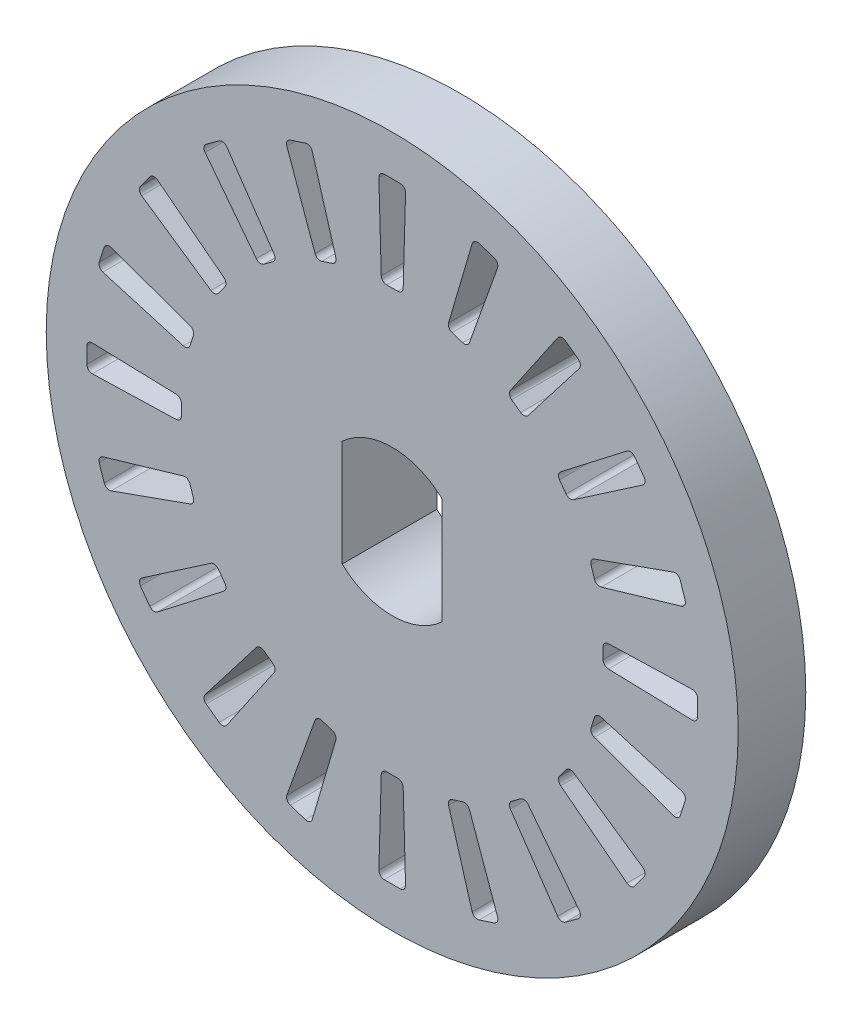
SolidWorks part; units mm, degrees
ref_plane "Alzado" through (0, 0, 0) normal (0, 0, 1) x (1, 0, 0)
ref_plane "Planta" through (0, 0, 0) normal (0, 1, 0) x (1, 0, 0)
ref_plane "Vista lateral" through (0, 0, 0) normal (1, 0, 0) x (0, 0, -1)
sketch "Croquis1" plane through (0, 0, 0) normal (0, 0, 1) x (1, 0, 0)
  line L0 (0, -5.4392) -> (0, 5.4392) construction
  line L1 (1.85, -1.9666) -> (1.85, 1.9666)
  line L2 (-1.85, -1.9666) -> (-1.85, 1.9666)
  line L3 (-1.85, -5.4392) -> (-1.85, 5.4392) construction
  line L4 (1.85, -5.4392) -> (1.85, 5.4392) construction
  circle A0 centre (0, 0) radius 12.8
  arc A1 (-1.85, -1.9666) -> (1.85, -1.9666) centre (0, 0) ccw
  arc A2 (1.85, 1.9666) -> (-1.85, 1.9666) centre (0, 0) ccw
  point P7 (0, 0)
  dimension "D1" = 25.6
  dimension "D2" = 5.4
  dimension "D3" = 1.85
  dimension "D4" = 1.85
extrude "Saliente-Extruir1" add sketch "Croquis1" along normal blind 2.5
sketch "Croquis2" plane through (0, 0, 0) normal (0, 0, 1) x (1, 0, 0)
  line L0 (-16.679, 12.8) -> (19.2749, 12.8) construction
  line L1 (0.2056, 7.8) -> (-0.2056, 7.8)
  line L2 (2.6059, 7.3547) -> (2.2148, 7.4818)
  line L3 (0.2942, 11.3) -> (-0.2942, 11.3)
  line L4 (3.7717, 10.656) -> (3.2121, 10.8379)
  line L5 (0.5, 7.8) -> (-0.5, 11.3) construction
  line L6 (0.5, 11.3) -> (-0.5, 7.8) construction
  line L7 (2.9584, 10.704) -> (2.0847, 7.7283)
  line L8 (3.8983, 10.3986) -> (2.8561, 7.4777)
  line L9 (-0.4941, 11.0943) -> (-0.4056, 7.9943)
  line L10 (0.4941, 11.0943) -> (0.4056, 7.9943)
  line L11 (2.8859, 7.2637) -> (3.0164, 10.9014) construction
  line L12 (3.9674, 10.5924) -> (1.9348, 7.5727) construction
  line L13 (4.7511, 6.1895) -> (4.4184, 6.4312)
  line L14 (6.88, 8.969) -> (6.404, 9.3148)
  line L15 (6.1213, 9.2659) -> (4.3708, 6.7059)
  line L16 (6.9208, 8.685) -> (5.027, 6.2291)
  line L17 (4.9892, 6.0164) -> (6.2375, 9.4358) construction
  line L18 (7.0465, 8.848) -> (4.1802, 6.6042) construction
  line L19 (6.4312, 4.4184) -> (6.1895, 4.7511)
  line L20 (9.3148, 6.404) -> (8.969, 6.88)
  line L21 (8.685, 6.9208) -> (6.2291, 5.027)
  line L22 (9.2659, 6.1213) -> (6.7059, 4.3708)
  line L23 (6.6042, 4.1802) -> (8.848, 7.0465) construction
  line L24 (9.4358, 6.2375) -> (6.0164, 4.9892) construction
  line L25 (7.4818, 2.2148) -> (7.3547, 2.6059)
  line L26 (10.8379, 3.2121) -> (10.656, 3.7717)
  line L27 (10.3986, 3.8983) -> (7.4777, 2.8561)
  line L28 (10.704, 2.9584) -> (7.7283, 2.0847)
  line L29 (7.5727, 1.9348) -> (10.5924, 3.9674) construction
  line L30 (10.9014, 3.0164) -> (7.2637, 2.8859) construction
  line L31 (7.8, -0.2056) -> (7.8, 0.2056)
  line L32 (11.3, -0.2942) -> (11.3, 0.2942)
  line L33 (11.0943, 0.4941) -> (7.9943, 0.4056)
  line L34 (11.0943, -0.4941) -> (7.9943, -0.4056)
  line L35 (7.8, -0.5) -> (11.3, 0.5) construction
  line L36 (11.3, -0.5) -> (7.8, 0.5) construction
  line L37 (7.3547, -2.6059) -> (7.4818, -2.2148)
  line L38 (10.656, -3.7717) -> (10.8379, -3.2121)
  line L39 (10.704, -2.9584) -> (7.7283, -2.0847)
  line L40 (10.3986, -3.8983) -> (7.4777, -2.8561)
  line L41 (7.2637, -2.8859) -> (10.9014, -3.0164) construction
  line L42 (10.5924, -3.9674) -> (7.5727, -1.9348) construction
  line L43 (6.1895, -4.7511) -> (6.4312, -4.4184)
  line L44 (8.969, -6.88) -> (9.3148, -6.404)
  line L45 (9.2659, -6.1213) -> (6.7059, -4.3708)
  line L46 (8.685, -6.9208) -> (6.2291, -5.027)
  line L47 (6.0164, -4.9892) -> (9.4358, -6.2375) construction
  line L48 (8.848, -7.0465) -> (6.6042, -4.1802) construction
  line L49 (4.4184, -6.4312) -> (4.7511, -6.1895)
  line L50 (6.404, -9.3148) -> (6.88, -8.969)
  line L51 (6.9208, -8.685) -> (5.027, -6.2291)
  line L52 (6.1213, -9.2659) -> (4.3708, -6.7059)
  line L53 (4.1802, -6.6042) -> (7.0465, -8.848) construction
  line L54 (6.2375, -9.4358) -> (4.9892, -6.0164) construction
  line L55 (2.2148, -7.4818) -> (2.6059, -7.3547)
  line L56 (3.2121, -10.8379) -> (3.7717, -10.656)
  line L57 (3.8983, -10.3986) -> (2.8561, -7.4777)
  line L58 (2.9584, -10.704) -> (2.0847, -7.7283)
  line L59 (1.9348, -7.5727) -> (3.9674, -10.5924) construction
  line L60 (3.0164, -10.9014) -> (2.8859, -7.2637) construction
  line L61 (-0.2056, -7.8) -> (0.2056, -7.8)
  line L62 (-0.2942, -11.3) -> (0.2942, -11.3)
  line L63 (0.4941, -11.0943) -> (0.4056, -7.9943)
  line L64 (-0.4941, -11.0943) -> (-0.4056, -7.9943)
  line L65 (-0.5, -7.8) -> (0.5, -11.3) construction
  line L66 (-0.5, -11.3) -> (0.5, -7.8) construction
  line L67 (-2.6059, -7.3547) -> (-2.2148, -7.4818)
  line L68 (-3.7717, -10.656) -> (-3.2121, -10.8379)
  line L69 (-2.9584, -10.704) -> (-2.0847, -7.7283)
  line L70 (-3.8983, -10.3986) -> (-2.8561, -7.4777)
  line L71 (-2.8859, -7.2637) -> (-3.0164, -10.9014) construction
  line L72 (-3.9674, -10.5924) -> (-1.9348, -7.5727) construction
  line L73 (-4.7511, -6.1895) -> (-4.4184, -6.4312)
  line L74 (-6.88, -8.969) -> (-6.404, -9.3148)
  line L75 (-6.1213, -9.2659) -> (-4.3708, -6.7059)
  line L76 (-6.9208, -8.685) -> (-5.027, -6.2291)
  line L77 (-4.9892, -6.0164) -> (-6.2375, -9.4358) construction
  line L78 (-7.0465, -8.848) -> (-4.1802, -6.6042) construction
  line L79 (-6.4312, -4.4184) -> (-6.1895, -4.7511)
  line L80 (-9.3148, -6.404) -> (-8.969, -6.88)
  line L81 (-8.685, -6.9208) -> (-6.2291, -5.027)
  line L82 (-9.2659, -6.1213) -> (-6.7059, -4.3708)
  line L83 (-6.6042, -4.1802) -> (-8.848, -7.0465) construction
  line L84 (-9.4358, -6.2375) -> (-6.0164, -4.9892) construction
  line L85 (-7.4818, -2.2148) -> (-7.3547, -2.6059)
  line L86 (-10.8379, -3.2121) -> (-10.656, -3.7717)
  line L87 (-10.3986, -3.8983) -> (-7.4777, -2.8561)
  line L88 (-10.704, -2.9584) -> (-7.7283, -2.0847)
  line L89 (-7.5727, -1.9348) -> (-10.5924, -3.9674) construction
  line L90 (-10.9014, -3.0164) -> (-7.2637, -2.8859) construction
  line L91 (-7.8, 0.2056) -> (-7.8, -0.2056)
  line L92 (-11.3, 0.2942) -> (-11.3, -0.2942)
  line L93 (-11.0943, -0.4941) -> (-7.9943, -0.4056)
  line L94 (-11.0943, 0.4941) -> (-7.9943, 0.4056)
  line L95 (-7.8, 0.5) -> (-11.3, -0.5) construction
  line L96 (-11.3, 0.5) -> (-7.8, -0.5) construction
  line L97 (-7.3547, 2.6059) -> (-7.4818, 2.2148)
  line L98 (-10.656, 3.7717) -> (-10.8379, 3.2121)
  line L99 (-10.704, 2.9584) -> (-7.7283, 2.0847)
  line L100 (-10.3986, 3.8983) -> (-7.4777, 2.8561)
  line L101 (-7.2637, 2.8859) -> (-10.9014, 3.0164) construction
  line L102 (-10.5924, 3.9674) -> (-7.5727, 1.9348) construction
  line L103 (-6.1895, 4.7511) -> (-6.4312, 4.4184)
  line L104 (-8.969, 6.88) -> (-9.3148, 6.404)
  line L105 (-9.2659, 6.1213) -> (-6.7059, 4.3708)
  line L106 (-8.685, 6.9208) -> (-6.2291, 5.027)
  line L107 (-6.0164, 4.9892) -> (-9.4358, 6.2375) construction
  line L108 (-8.848, 7.0465) -> (-6.6042, 4.1802) construction
  line L109 (-4.4184, 6.4312) -> (-4.7511, 6.1895)
  line L110 (-6.404, 9.3148) -> (-6.88, 8.969)
  line L111 (-6.9208, 8.685) -> (-5.027, 6.2291)
  line L112 (-6.1213, 9.2659) -> (-4.3708, 6.7059)
  line L113 (-4.1802, 6.6042) -> (-7.0465, 8.848) construction
  line L114 (-6.2375, 9.4358) -> (-4.9892, 6.0164) construction
  line L115 (-2.2148, 7.4818) -> (-2.6059, 7.3547)
  line L116 (-3.2121, 10.8379) -> (-3.7717, 10.656)
  line L117 (-3.8983, 10.3986) -> (-2.8561, 7.4777)
  line L118 (-2.9584, 10.704) -> (-2.0847, 7.7283)
  line L119 (-1.9348, 7.5727) -> (-3.9674, 10.5924) construction
  line L120 (-3.0164, 10.9014) -> (-2.8859, 7.2637) construction
  arc A0 (0.2056, 7.8) -> (0.4056, 7.9943) centre (0.2056, 8) ccw
  circle A1 centre (0, 0) radius 12.8 construction
  arc A2 (-0.2056, 7.8) -> (-0.4056, 7.9943) centre (-0.2056, 8) cw
  arc A3 (0.4941, 11.0943) -> (0.2942, 11.3) centre (0.2942, 11.1) ccw
  arc A4 (-0.2942, 11.3) -> (-0.4941, 11.0943) centre (-0.2942, 11.1) ccw
  arc A5 (2.6059, 7.3547) -> (2.8561, 7.4777) centre (2.6677, 7.5449) ccw
  arc A6 (2.2148, 7.4818) -> (2.0847, 7.7283) centre (2.2766, 7.672) cw
  arc A7 (3.8983, 10.3986) -> (3.7717, 10.656) centre (3.7099, 10.4658) ccw
  arc A8 (3.2121, 10.8379) -> (2.9584, 10.704) centre (3.1503, 10.6476) ccw
  arc A9 (4.7511, 6.1895) -> (5.027, 6.2291) centre (4.8686, 6.3513) ccw
  arc A10 (4.4184, 6.4312) -> (4.3708, 6.7059) centre (4.5359, 6.593) cw
  arc A11 (6.9208, 8.685) -> (6.88, 8.969) centre (6.7624, 8.8072) ccw
  arc A12 (6.404, 9.3148) -> (6.1213, 9.2659) centre (6.2864, 9.153) ccw
  arc A13 (6.4312, 4.4184) -> (6.7059, 4.3708) centre (6.593, 4.5359) ccw
  arc A14 (6.1895, 4.7511) -> (6.2291, 5.027) centre (6.3513, 4.8686) cw
  arc A15 (9.2659, 6.1213) -> (9.3148, 6.404) centre (9.153, 6.2864) ccw
  arc A16 (8.969, 6.88) -> (8.685, 6.9208) centre (8.8072, 6.7624) ccw
  arc A17 (7.4818, 2.2148) -> (7.7283, 2.0847) centre (7.672, 2.2766) ccw
  arc A18 (7.3547, 2.6059) -> (7.4777, 2.8561) centre (7.5449, 2.6677) cw
  arc A19 (10.704, 2.9584) -> (10.8379, 3.2121) centre (10.6476, 3.1503) ccw
  arc A20 (10.656, 3.7717) -> (10.3986, 3.8983) centre (10.4658, 3.7099) ccw
  arc A21 (7.8, -0.2056) -> (7.9943, -0.4056) centre (8, -0.2056) ccw
  arc A22 (7.8, 0.2056) -> (7.9943, 0.4056) centre (8, 0.2056) cw
  arc A23 (11.0943, -0.4941) -> (11.3, -0.2942) centre (11.1, -0.2942) ccw
  arc A24 (11.3, 0.2942) -> (11.0943, 0.4941) centre (11.1, 0.2942) ccw
  arc A25 (7.3547, -2.6059) -> (7.4777, -2.8561) centre (7.5449, -2.6677) ccw
  arc A26 (7.4818, -2.2148) -> (7.7283, -2.0847) centre (7.672, -2.2766) cw
  arc A27 (10.3986, -3.8983) -> (10.656, -3.7717) centre (10.4658, -3.7099) ccw
  arc A28 (10.8379, -3.2121) -> (10.704, -2.9584) centre (10.6476, -3.1503) ccw
  arc A29 (6.1895, -4.7511) -> (6.2291, -5.027) centre (6.3513, -4.8686) ccw
  arc A30 (6.4312, -4.4184) -> (6.7059, -4.3708) centre (6.593, -4.5359) cw
  arc A31 (8.685, -6.9208) -> (8.969, -6.88) centre (8.8072, -6.7624) ccw
  arc A32 (9.3148, -6.404) -> (9.2659, -6.1213) centre (9.153, -6.2864) ccw
  arc A33 (4.4184, -6.4312) -> (4.3708, -6.7059) centre (4.5359, -6.593) ccw
  arc A34 (4.7511, -6.1895) -> (5.027, -6.2291) centre (4.8686, -6.3513) cw
  arc A35 (6.1213, -9.2659) -> (6.404, -9.3148) centre (6.2864, -9.153) ccw
  arc A36 (6.88, -8.969) -> (6.9208, -8.685) centre (6.7624, -8.8072) ccw
  arc A37 (2.2148, -7.4818) -> (2.0847, -7.7283) centre (2.2766, -7.672) ccw
  arc A38 (2.6059, -7.3547) -> (2.8561, -7.4777) centre (2.6677, -7.5449) cw
  arc A39 (2.9584, -10.704) -> (3.2121, -10.8379) centre (3.1503, -10.6476) ccw
  arc A40 (3.7717, -10.656) -> (3.8983, -10.3986) centre (3.7099, -10.4658) ccw
  arc A41 (-0.2056, -7.8) -> (-0.4056, -7.9943) centre (-0.2056, -8) ccw
  arc A42 (0.2056, -7.8) -> (0.4056, -7.9943) centre (0.2056, -8) cw
  arc A43 (-0.4941, -11.0943) -> (-0.2942, -11.3) centre (-0.2942, -11.1) ccw
  arc A44 (0.2942, -11.3) -> (0.4941, -11.0943) centre (0.2942, -11.1) ccw
  arc A45 (-2.6059, -7.3547) -> (-2.8561, -7.4777) centre (-2.6677, -7.5449) ccw
  arc A46 (-2.2148, -7.4818) -> (-2.0847, -7.7283) centre (-2.2766, -7.672) cw
  arc A47 (-3.8983, -10.3986) -> (-3.7717, -10.656) centre (-3.7099, -10.4658) ccw
  arc A48 (-3.2121, -10.8379) -> (-2.9584, -10.704) centre (-3.1503, -10.6476) ccw
  arc A49 (-4.7511, -6.1895) -> (-5.027, -6.2291) centre (-4.8686, -6.3513) ccw
  arc A50 (-4.4184, -6.4312) -> (-4.3708, -6.7059) centre (-4.5359, -6.593) cw
  arc A51 (-6.9208, -8.685) -> (-6.88, -8.969) centre (-6.7624, -8.8072) ccw
  arc A52 (-6.404, -9.3148) -> (-6.1213, -9.2659) centre (-6.2864, -9.153) ccw
  arc A53 (-6.4312, -4.4184) -> (-6.7059, -4.3708) centre (-6.593, -4.5359) ccw
  arc A54 (-6.1895, -4.7511) -> (-6.2291, -5.027) centre (-6.3513, -4.8686) cw
  arc A55 (-9.2659, -6.1213) -> (-9.3148, -6.404) centre (-9.153, -6.2864) ccw
  arc A56 (-8.969, -6.88) -> (-8.685, -6.9208) centre (-8.8072, -6.7624) ccw
  arc A57 (-7.4818, -2.2148) -> (-7.7283, -2.0847) centre (-7.672, -2.2766) ccw
  arc A58 (-7.3547, -2.6059) -> (-7.4777, -2.8561) centre (-7.5449, -2.6677) cw
  arc A59 (-10.704, -2.9584) -> (-10.8379, -3.2121) centre (-10.6476, -3.1503) ccw
  arc A60 (-10.656, -3.7717) -> (-10.3986, -3.8983) centre (-10.4658, -3.7099) ccw
  arc A61 (-7.8, 0.2056) -> (-7.9943, 0.4056) centre (-8, 0.2056) ccw
  arc A62 (-7.8, -0.2056) -> (-7.9943, -0.4056) centre (-8, -0.2056) cw
  arc A63 (-11.0943, 0.4941) -> (-11.3, 0.2942) centre (-11.1, 0.2942) ccw
  arc A64 (-11.3, -0.2942) -> (-11.0943, -0.4941) centre (-11.1, -0.2942) ccw
  arc A65 (-7.3547, 2.6059) -> (-7.4777, 2.8561) centre (-7.5449, 2.6677) ccw
  arc A66 (-7.4818, 2.2148) -> (-7.7283, 2.0847) centre (-7.672, 2.2766) cw
  arc A67 (-10.3986, 3.8983) -> (-10.656, 3.7717) centre (-10.4658, 3.7099) ccw
  arc A68 (-10.8379, 3.2121) -> (-10.704, 2.9584) centre (-10.6476, 3.1503) ccw
  arc A69 (-6.1895, 4.7511) -> (-6.2291, 5.027) centre (-6.3513, 4.8686) ccw
  arc A70 (-6.4312, 4.4184) -> (-6.7059, 4.3708) centre (-6.593, 4.5359) cw
  arc A71 (-8.685, 6.9208) -> (-8.969, 6.88) centre (-8.8072, 6.7624) ccw
  arc A72 (-9.3148, 6.404) -> (-9.2659, 6.1213) centre (-9.153, 6.2864) ccw
  arc A73 (-4.4184, 6.4312) -> (-4.3708, 6.7059) centre (-4.5359, 6.593) ccw
  arc A74 (-4.7511, 6.1895) -> (-5.027, 6.2291) centre (-4.8686, 6.3513) cw
  arc A75 (-6.1213, 9.2659) -> (-6.404, 9.3148) centre (-6.2864, 9.153) ccw
  arc A76 (-6.88, 8.969) -> (-6.9208, 8.685) centre (-6.7624, 8.8072) ccw
  arc A77 (-2.2148, 7.4818) -> (-2.0847, 7.7283) centre (-2.2766, 7.672) ccw
  arc A78 (-2.6059, 7.3547) -> (-2.8561, 7.4777) centre (-2.6677, 7.5449) cw
  arc A79 (-2.9584, 10.704) -> (-3.2121, 10.8379) centre (-3.1503, 10.6476) ccw
  arc A80 (-3.7717, 10.656) -> (-3.8983, 10.3986) centre (-3.7099, 10.4658) ccw
  point P0 (0, 9.55)
  point P8 (0, 11.3)
  point P15 (0.4, 7.8)
  point P18 (-0.4, 7.8)
  point P28 (2.9511, 9.0826)
  point P45 (5.6133, 7.7261)
  point P62 (7.7261, 5.6133)
  point P79 (9.0826, 2.9511)
  point P96 (9.55, 0)
  point P113 (9.0826, -2.9511)
  point P130 (7.7261, -5.6133)
  point P147 (5.6133, -7.7261)
  point P164 (2.9511, -9.0826)
  point P181 (0, -9.55)
  point P198 (-2.9511, -9.0826)
  point P215 (-5.6133, -7.7261)
  point P232 (-7.7261, -5.6133)
  point P249 (-9.0826, -2.9511)
  point P266 (-9.55, 0)
  point P283 (-9.0826, 2.9511)
  point P300 (-7.7261, 5.6133)
  point P317 (-5.6133, 7.7261)
  point P334 (-2.9511, 9.0826)
  point P351 (0, 0)
  dimension "D5" = 0.2
  dimension "D1" = 3.5
  dimension "D2" = 1
  dimension "D3" = 1.5
  dimension "D6" = 0.4113
  dimension "D4" = 0.8
  dimension "D7" = 20
extrude "Cortar-Extruir1" cut sketch "Croquis2" along normal blind 7.5
sketch "Croquis3" plane through (0, 0, 0) normal (0, 0, -1) x (-1, 0, 0)
  line L4 (1.85, -1.9666) -> (1.85, 1.9666)
  line L5 (-1.85, 1.9666) -> (-1.85, -1.9666)
  line L6 (2.85, -2.3596) -> (2.85, 2.3596)
  line L7 (-2.85, 2.3596) -> (-2.85, -2.3596)
  line L8 (2.85, -2.3596) -> (2.85, 2.3596)
  line L9 (-2.85, 2.3596) -> (-2.85, -2.3596)
  arc A4 (1.85, 1.9666) -> (-1.85, 1.9666) centre (0, 0) ccw
  arc A5 (-1.85, -1.9666) -> (1.85, -1.9666) centre (0, 0) ccw
  arc A6 (-2.85, -2.3596) -> (2.85, -2.3596) centre (0, 0) ccw
  arc A7 (2.85, 2.3596) -> (-2.85, 2.3596) centre (0, 0) ccw
  arc A8 (-2.85, -2.3596) -> (2.85, -2.3596) centre (0, 0) ccw
  arc A9 (2.85, 2.3596) -> (-2.85, 2.3596) centre (0, 0) ccw
  dimension "D1" = 1
  dimension "D2" = 1
extrude "Saliente-Extruir2" add sketch "Croquis3" along normal blind 1
